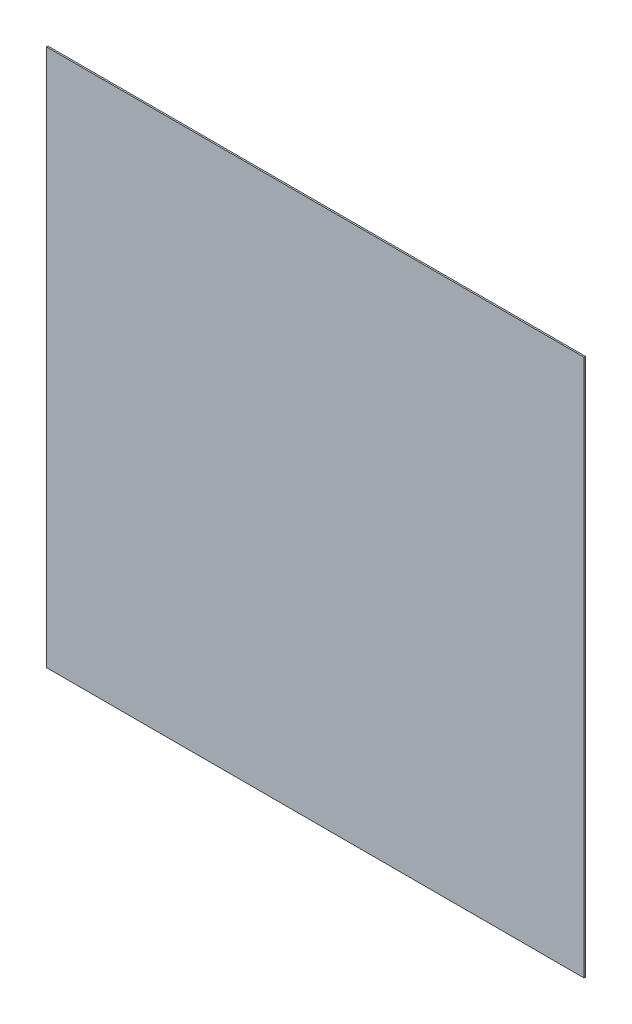
SolidWorks part; units mm, degrees
ref_plane "Front" through (0, 0, 0) normal (0, 0, 1) x (1, 0, 0)
ref_plane "Top" through (0, 0, 0) normal (0, 1, 0) x (1, 0, 0)
ref_plane "Right" through (0, 0, 0) normal (1, 0, 0) x (0, 0, -1)
sketch "Sketch1" plane through (0, 0, 0) normal (0, 0, 1) x (1, 0, 0)
  line L1 (-360, 360) -> (360, 360)
  line L2 (-360, 360) -> (-360, -360)
  line L3 (-360, -360) -> (360, -360)
  line L4 (360, 360) -> (360, -360)
  line L5 (-360, 360) -> (360, -360) construction
  line L6 (-360, -360) -> (360, 360) construction
  point P0 (0, 0)
  dimension "D1" = 720
  dimension "D2" = 720
extrude "Boss-Extrude1" add sketch "Sketch1" along normal blind 2
sketch "Sketch2" plane through (0, 0, 0) normal (0, 0, -1) x (-1, 0, 0)
  line L0 (-360, 360) -> (360, 360) construction
  line L2 (-91.4177, 0) -> (78.2357, 0) construction
  line L3 (0, 61.169) -> (0, -78.8952) construction
  line L4 (-360, -360) -> (-360, 360) construction
  circle A0 centre (0, 340) radius 5
  circle A1 centre (-340, 0) radius 5
  circle A2 centre (0, -340) radius 5
  circle A3 centre (340, 0) radius 5
  dimension "D1" = 10
  dimension "D4" = 10
  dimension "D2" = 20
  dimension "D3" = 0
  dimension "D5" = 20
  dimension "D6" = 0
extrude "Boss-Extrude2" add sketch "Sketch2" along normal blind 2
